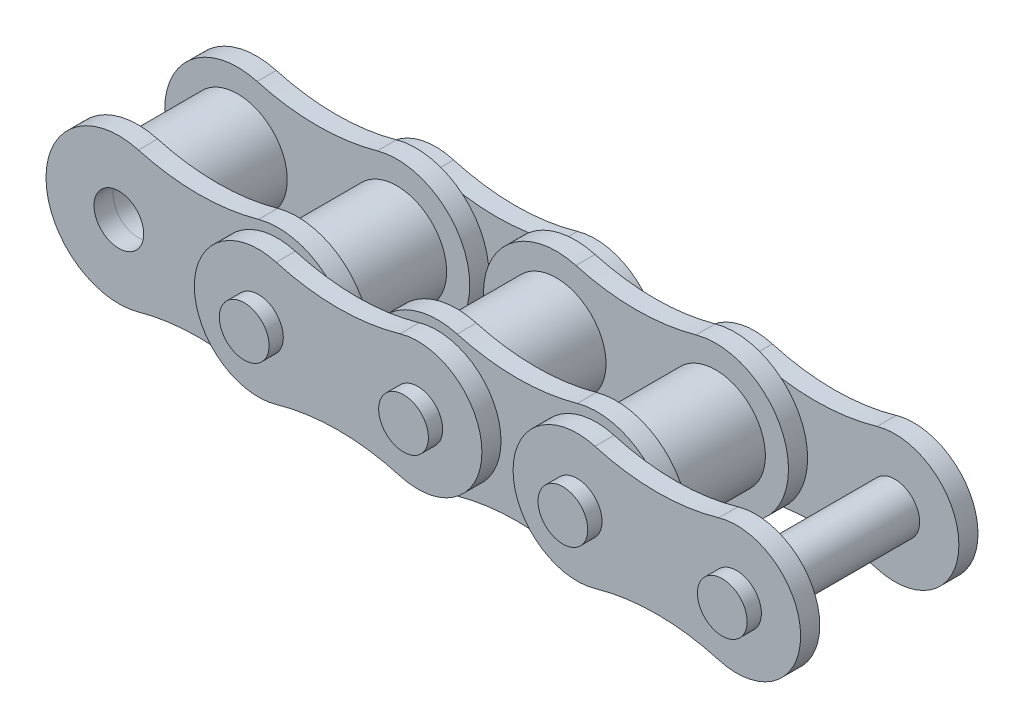
SolidWorks part; units mm, degrees
ref_plane "Front Plane" through (0, 0, 0) normal (0, 0, 1) x (1, 0, 0)
ref_plane "Top Plane" through (0, 0, 0) normal (0, 1, 0) x (1, 0, 0)
ref_plane "Right Plane" through (0, 0, 0) normal (1, 0, 0) x (0, 0, -1)
sketch "Sketch1" plane through (0, 0, 0) normal (0, 0, 1) x (1, 0, 0)
  line L0 (-6.35, 0) -> (6.35, 0) construction
  line L1 (-6.35, 5.8039) -> (-6.35, -5.8039) construction
  line L2 (0, -4.9333) -> (0, 4.9333) construction
  circle A0 centre (-6.35, 0) radius 3.9624
  circle A1 centre (6.35, 0) radius 3.9624
  circle A2 centre (-6.35, 0) radius 1.9812
  circle A3 centre (6.35, 0) radius 1.9812
  arc A4 (-4.7879, 5.5897) -> (-4.7879, -5.5897) centre (-6.35, 0) ccw
  arc A5 (4.7879, -5.5897) -> (4.7879, 5.5897) centre (6.35, 0) ccw
  arc A6 (-4.7879, 5.5897) -> (4.7879, 5.5897) centre (0, 22.723) ccw
  arc A7 (-4.7879, -5.5897) -> (4.7879, -5.5897) centre (0, -22.723) cw
  dimension "Roller Dia" = 7.9248
  dimension "Pin Dia" = 3.9624
  dimension "Pitch" = 12.7
  dimension "H" = 11.6078
  dimension "D2" = 9.8666
sketch "Sketch2" plane through (0, 0, 0) normal (0, 1, 0) x (1, 0, 0)
  line L0 (0, 3.9688) -> (0, -3.9688) construction
  point P2 (0, -5.4928)
  point P4 (0, 5.4928)
  point P5 (0, 5.5436)
  point P6 (0, 7.0676)
  dimension "D1" = 1.524
  dimension "W" = 7.9375
  dimension "T" = 1.524
  dimension "D2" = 1.524
  dimension "D3" = 0.0508
ref_plane "Plane1" through (0, 0, 3.9688) normal (0, 0, 1) x (1, 0, 0)
ref_plane "Plane2" through (0, 0, -5.5436) normal (0, 0, 1) x (1, 0, 0)
sketch "Sketch4" plane through (0, 0, 0) normal (0, 0, 1) x (1, 0, 0)
  circle A0 centre (-6.35, 0) radius 3.9624 construction
  circle A1 centre (-6.35, 0) radius 3.9624
  circle A2 centre (6.35, 0) radius 3.9624 construction
  circle A3 centre (6.35, 0) radius 3.9624
  circle A4 centre (-6.35, 0) radius 2.0066
  circle A5 centre (6.35, 0) radius 2.0066
  dimension "D1" = 4.0132
  dimension "D2" = 4.0132
extrude "Boss-Extrude1" add sketch "Sketch4" along normal mid plane 7.9375
sketch "Sketch5" plane through (0, 0, 3.9688) normal (0, 0, 1) x (1, 0, 0)
  arc A0 (-4.7879, 5.5897) -> (-4.7879, -5.5897) centre (-6.35, 0) ccw construction
  arc A1 (-4.7879, 5.5897) -> (4.7879, 5.5897) centre (0, 22.723) ccw construction
  circle A2 centre (-6.35, 0) radius 1.9812 construction
  arc A3 (4.7879, -5.5897) -> (4.7879, 5.5897) centre (6.35, 0) ccw construction
  circle A4 centre (6.35, 0) radius 1.9812 construction
  arc A5 (4.7879, -5.5897) -> (-4.7879, -5.5897) centre (0, -22.723) ccw construction
  arc A6 (-4.7879, 5.5897) -> (-4.7879, -5.5897) centre (-6.35, 0) ccw
  arc A7 (-4.7879, 5.5897) -> (4.7879, 5.5897) centre (0, 22.723) ccw
  circle A8 centre (-6.35, 0) radius 1.9812
  arc A9 (4.7879, -5.5897) -> (4.7879, 5.5897) centre (6.35, 0) ccw
  circle A10 centre (6.35, 0) radius 1.9812
  arc A11 (4.7879, -5.5897) -> (-4.7879, -5.5897) centre (0, -22.723) ccw
extrude "Boss-Extrude2" add sketch "Sketch5" along normal up to vertex (1.524 mm away) separate body up to point (0, 0, 5.4928)
pattern_linear "LPattern1" count 2 spacing 12.7 along (1, 0, 0) of bodies 102
sketch "Sketch7" plane through (0, 0, -5.5436) normal (0, 0, 1) x (1, 0, 0)
  line L0 (19.05, 5.1074) -> (19.05, -5.1074) construction
  arc A0 (7.7664, 4.9071) -> (7.7664, -4.9071) centre (6.35, 0) ccw
  arc A1 (17.6336, -4.9071) -> (17.6336, 4.9071) centre (19.05, 0) ccw
  arc A2 (4.7879, -5.5897) -> (4.7879, 5.5897) centre (6.35, 0) ccw construction
  circle A3 centre (19.05, 0) radius 3.9624 construction
  arc A4 (7.7664, 4.9071) -> (17.6336, 4.9071) centre (12.7, 21.999) ccw
  arc A5 (7.7664, -4.9071) -> (17.6336, -4.9071) centre (12.7, -21.999) cw
  arc A6 (-4.7879, 5.5897) -> (4.7879, 5.5897) centre (0, 22.723) ccw construction
  circle A7 centre (6.35, 0) radius 1.9812 construction
  circle A8 centre (6.35, 0) radius 1.9812
  circle A9 centre (19.05, 0) radius 1.9812
  dimension "D2" = 10.2149
extrude "Boss-Extrude3" add sketch "Sketch7" against normal up to vertex (1.524 mm away) separate body up to point (0, 0, -7.0676)
mirror "Mirror1" about plane through (0, 0, 0) normal (0, 0, 1) of bodies 103 105
sketch "Sketch8" plane through (0, 0, 0) normal (0, 0, 1) x (1, 0, 0)
  circle A0 centre (6.35, 0) radius 1.9812
  circle A1 centre (19.05, 0) radius 1.9812
  circle A2 centre (6.35, 0) radius 1.9812 construction
  circle A3 centre (19.05, 0) radius 1.9812 construction
extrude "Boss-Extrude4" add sketch "Sketch8" against normal blind 8.2042 and the other way blind 8.2042 separate body
pattern_linear "LPattern2" count 2 spacing 25.4 along (1, 0, 0) of bodies 109 108 107 106 105 104 103 102 101
delete or keep bodies "Body-Delete1" type delete bodies bodies 115
combine bodies "Combine1" operation type add bodies to combine 102 103 104 105 106 107 108 109 110 111 112 113 114 116 117 118 101
sketch "Sketch9" plane through (0, 0, 0) normal (0, 0, 1) x (1, 0, 0)
  line L0 (44.45, 5.1074) -> (44.45, -5.1074) construction
  line L1 (31.75, 5.8039) -> (31.75, -5.8039) construction
  arc A0 (30.1879, -5.5897) -> (30.1879, 5.5897) centre (31.75, 0) ccw construction
  arc A1 (31.75, -5.8039) -> (31.75, 5.8039) centre (31.75, 0) ccw
  arc A2 (43.0336, -4.9071) -> (43.0336, 4.9071) centre (44.45, 0) ccw construction
  arc A3 (44.45, -5.1074) -> (44.45, 5.1074) centre (44.45, 0) ccw
  circle A4 centre (-6.35, 0) radius 3.9624 construction
  circle A5 centre (-6.35, 0) radius 3.9624
equation "\"D2@Sketch1\" =\"H@Sketch1\"*.85"
equation "\"D1@Sketch2\" = \"T@Sketch2\""
equation "\"D1@Sketch4\" = \"Pin Dia@Sketch1\"+.002"
equation "\"D2@Sketch4\" = \"D1@Sketch4\""
equation "\"D1@Boss-Extrude1\" = \"W@Sketch2\""
equation "\"D2@Sketch2\" = \"T@Sketch2\""
equation "\"D3@LPattern1\" = \"Pitch@Sketch1\""
equation "\"D3@LPattern2\" = \"Pitch@Sketch1\"*2"
equation "\"D2@Sketch7\" = \"H@Sketch1\"*.88"
